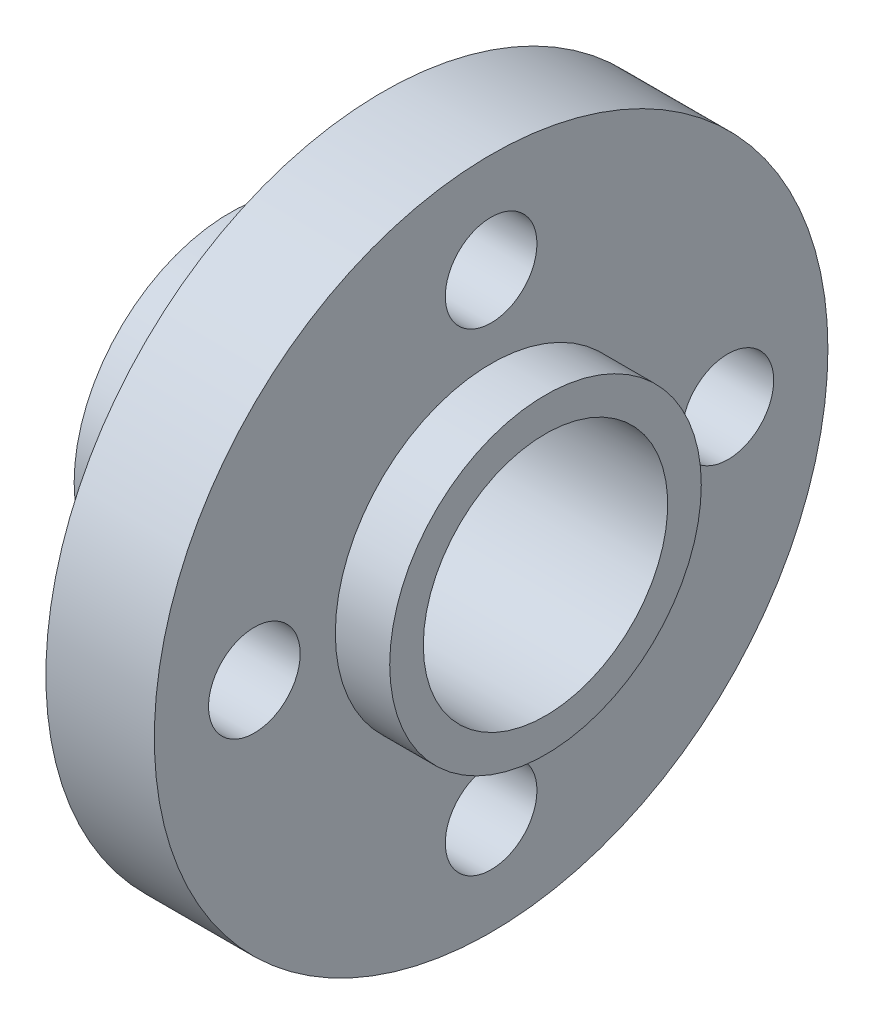
SolidWorks part; units mm, degrees
material "Brass"
ref_plane "Front Plane" through (0, 0, 0) normal (0, 0, 1) x (1, 0, 0)
ref_plane "Top Plane" through (0, 0, 0) normal (0, 1, 0) x (1, 0, 0)
ref_plane "Right Plane" through (0, 0, 0) normal (1, 0, 0) x (0, 0, -1)
sketch "Sketch1" plane through (0, 0, 0) normal (1, 0, 0) x (0, 0, -1)
  circle A0 centre (0, 0) radius 11.025
  dimension "D1" = 22.05
extrude "Boss-Extrude1" add sketch "Sketch1" along normal blind 3.55
sketch "Sketch2" plane through (3.55, 0, 0) normal (1, 0, 0) x (0, 0, -1)
  circle A0 centre (0, 0) radius 5.1
  dimension "D1" = 10.2
extrude "Boss-Extrude2" add sketch "Sketch2" along normal blind 1.78
sketch "Sketch3" plane through (0, 0, 0) normal (-1, 0, 0) x (0, 0, 1)
  circle A0 centre (0, 0) radius 5.1
  dimension "D1" = 10.2
extrude "Boss-Extrude3" add sketch "Sketch3" along normal blind 5
sketch "Sketch5" plane through (-5, 0, 0) normal (-1, 0, 0) x (0, 0, 1)
  circle A0 centre (0, 0) radius 4
  dimension "D1" = 8
extrude "Cut-Extrude1" cut sketch "Sketch5" against normal through all
sketch "Sketch6" plane through (0, 0, 0) normal (-1, 0, 0) x (0, 0, 1)
  circle A0 centre (0, 0) radius 7.75 construction
  circle A1 centre (-7.75, 0) radius 1.5
  dimension "D1" = 15.5
  dimension "D2" = 3
extrude "Cut-Extrude2" cut sketch "Sketch6" against normal through all
pattern_circular "CirPattern1" count 4 over 360 about axis through (0, 0, 0) along (1, 0, 0) of "Cut-Extrude2"
